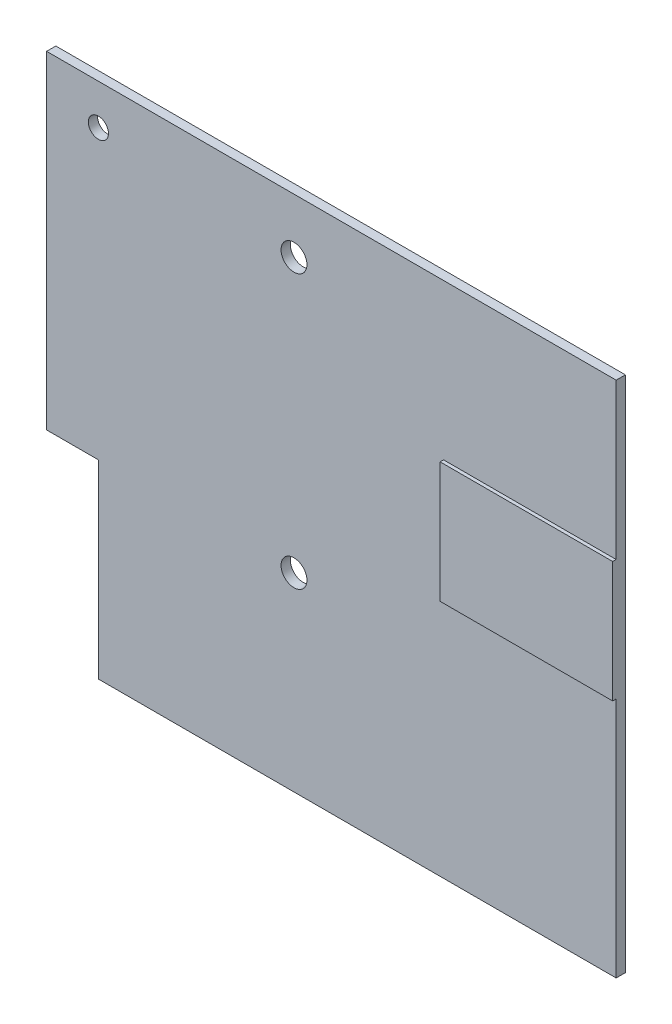
SolidWorks part; units mm, degrees
material "ABS"
ref_plane "Front Plane" through (0, 0, 0) normal (0, 0, 1) x (1, 0, 0)
ref_plane "Top Plane" through (0, 0, 0) normal (0, 1, 0) x (1, 0, 0)
ref_plane "Right Plane" through (0, 0, 0) normal (1, 0, 0) x (0, 0, -1)
sketch "Sketch1" plane through (0, 0, 0) normal (0, 0, 1) x (1, 0, 0)
  line L1 (9, 0) -> (99, 0)
  line L2 (0, 33) -> (0, 90)
  line L3 (0, 90) -> (99, 90)
  line L4 (99, 0) -> (99, 90)
  line L7 (0, 33) -> (9, 33)
  line L8 (9, 0) -> (9, 33)
  dimension "D1" = 99
  dimension "D2" = 90
  dimension "D3" = 0
  dimension "D4" = 0
  dimension "D5" = 33
  dimension "D6" = 9
extrude "BoardBase" add sketch "Sketch1" against normal blind 1.6 contours L3 L4 L1 L8 L7 L2
sketch "Sketch2" plane through (0, 0, 0) normal (0, 0, 1) x (1, 0, 0)
  line L0 (9, 0) -> (99, 0) construction
  line L1 (0, 33) -> (0, 90) construction
  circle A0 centre (9, 83) radius 1.75
  circle A1 centre (43, 80.5) radius 2.25
  circle A2 centre (43, 33) radius 2.25
  dimension "D1" = 3.5
  dimension "D3" = 9
  dimension "D4" = 4.5
  dimension "D5" = 4.5
  dimension "D2" = 83
  dimension "D6" = 33
  dimension "D7" = 47.5
  dimension "D8" = 43
  dimension "D9" = 43
extrude "Existing Holes" cut sketch "Sketch2" against normal through all
sketch "Sketch3" plane through (0, 0, 0) normal (0, 0, 1) x (1, 0, 0)
  line L0 (99, 0) -> (99, 90) construction
  line L1 (99, 63) -> (69, 63)
  line L2 (99, 63) -> (99, 42)
  line L3 (99, 42) -> (69, 42)
  line L4 (69, 63) -> (69, 42)
  line L5 (9, 0) -> (99, 0) construction
  dimension "D1" = 63
  dimension "D2" = 42
  dimension "D3" = 30
extrude "'Free' area" add sketch "Sketch3" along normal blind 0.6
